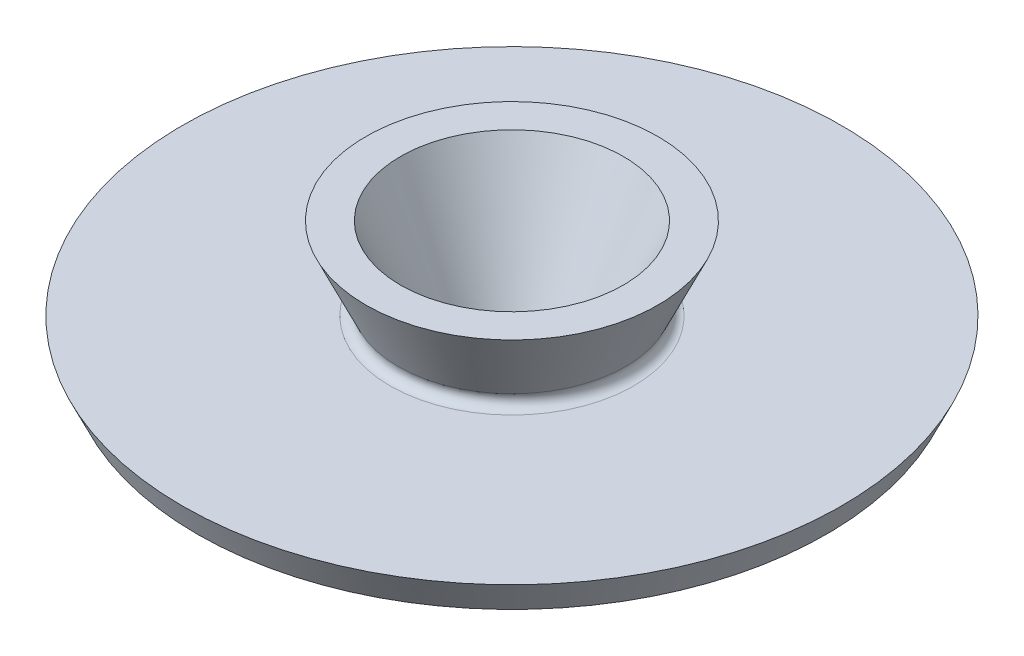
SolidWorks part; units mm, degrees
ref_plane "Front Plane" through (0, 0, 0) normal (0, 0, 1) x (1, 0, 0)
ref_plane "Top Plane" through (0, 0, 0) normal (0, 1, 0) x (1, 0, 0)
ref_plane "Right Plane" through (0, 0, 0) normal (1, 0, 0) x (0, 0, -1)
sketch "Sketch1" plane through (0, 0, 0) normal (0, 0, 1) x (1, 0, 0)
  line L0 (0, 77.136) -> (0, -50.6077) construction
  line L1 (-93.6738, 4.4894) -> (-89.447, -4.5752)
  line L2 (-89.447, -4.5752) -> (-20.4735, -4.5752)
  line L3 (-20.4735, -4.5752) -> (-17.8286, -10.2472)
  line L5 (-93.6738, 4.4894) -> (-34.6028, 4.4894)
  line L6 (-32.3008, 8.1028) -> (-41.5103, 27.8528)
  line L7 (-41.5103, 27.8528) -> (-31.6856, 27.8528)
  line L8 (-31.6856, 27.8528) -> (-13.9193, -10.2472)
  line L11 (-17.8286, -10.2472) -> (-13.9193, -10.2472)
  arc A0 (-32.3008, 8.1028) -> (-34.6028, 4.4894) centre (-34.6028, 7.0294) cw
  point P8 (-11.3241, -15.8127)
  dimension "D1" = 2.54
  dimension "D2" = 25
  dimension "D3" = 3.543
  dimension "0.375" = 57.15
  dimension "D4" = 38.1
revolve "Revolve2" add sketch "Sketch1" angle 360 about L0
